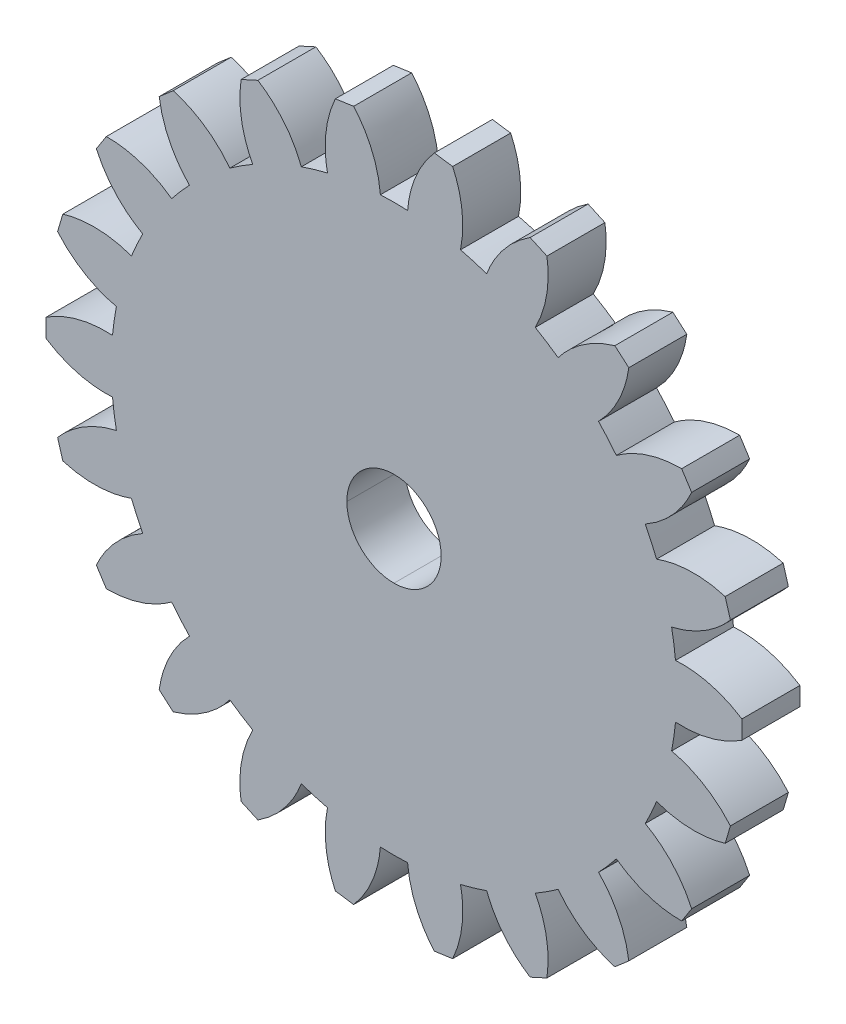
SolidWorks part; units mm, degrees
ref_plane "Alzado" through (0, 0, 0) normal (0, 0, 1) x (1, 0, 0)
ref_plane "Planta" through (0, 0, 0) normal (0, 1, 0) x (1, 0, 0)
ref_plane "Vista lateral" through (0, 0, 0) normal (1, 0, 0) x (0, 0, -1)
sketch "Croquis1" plane through (0, 0, 0) normal (0, 0, 1) x (1, 0, 0)
  spline S120 degree 3 poles (403.5425, -328.4425) (403.5425, -326.6476) (404.9976, -325.1925) (406.7925, -325.1925) knots 0 0 0 0 1 1 1 1
  spline S121 degree 3 poles (406.7925, -325.1925) (408.5874, -325.1925) (410.0425, -326.6476) (410.0425, -328.4425) knots 1 1 1 1 2 2 2 2
  spline S122 degree 3 poles (410.0425, -328.4425) (410.0425, -330.2374) (408.5874, -331.6925) (406.7925, -331.6925) knots 2 2 2 2 3 3 3 3
  spline S123 degree 3 poles (406.7925, -331.6925) (404.9976, -331.6925) (403.5425, -330.2374) (403.5425, -328.4425) knots 3 3 3 3 4 4 4 4
  spline S124 degree 3 poles (396.2468, -350.0015) (396.6282, -350.188) (397.0145, -350.3644) (397.4053, -350.5305) knots 0 0 0 0 1 1 1 1
  spline S125 degree 3 poles (397.4053, -350.5305) (398.7735, -349.6639) (399.8253, -348.3789) (400.4043, -346.8664) knots 0 0 0 0 1 1 1 1
  spline S126 degree 3 poles (400.4043, -346.8664) (400.996, -347.0716) (401.5972, -347.2481) (402.2059, -347.3954) knots 0 0 0 0 1 1 1 1
  spline S127 degree 3 poles (402.2059, -347.3954) (401.8754, -348.9808) (402.0654, -350.6306) (402.7479, -352.0992) knots 0 0 0 0 1 1 1 1
  spline S128 degree 3 poles (402.7479, -352.0992) (403.1664, -352.1708) (403.5868, -352.2312) (404.0085, -352.2805) knots 0 0 0 0 1 1 1 1
  spline S129 degree 3 poles (404.0085, -352.2805) (405.077, -351.0636) (405.7242, -349.5342) (405.8536, -347.9199) knots 0 0 0 0 1 1 1 1
  spline S130 degree 3 poles (405.8536, -347.9199) (406.4792, -347.95) (407.1059, -347.95) (407.7314, -347.9199) knots 0 0 0 0 1 1 1 1
  spline S131 degree 3 poles (407.7314, -347.9199) (407.8608, -349.5342) (408.508, -351.0636) (409.5766, -352.2805) knots 0 0 0 0 1 1 1 1
  spline S132 degree 3 poles (409.5766, -352.2805) (409.9983, -352.2312) (410.4186, -352.1708) (410.8372, -352.0992) knots 0 0 0 0 1 1 1 1
  spline S133 degree 3 poles (410.8372, -352.0992) (411.5196, -350.6306) (411.7097, -348.9808) (411.3791, -347.3954) knots 0 0 0 0 1 1 1 1
  spline S134 degree 3 poles (411.3791, -347.3954) (411.9878, -347.2481) (412.5891, -347.0716) (413.1808, -346.8664) knots 0 0 0 0 1 1 1 1
  spline S135 degree 3 poles (413.1808, -346.8664) (413.7598, -348.3789) (414.8116, -349.6639) (416.1798, -350.5305) knots 0 0 0 0 1 1 1 1
  spline S136 degree 3 poles (416.1798, -350.5305) (416.5705, -350.3644) (416.9568, -350.188) (417.3382, -350.0015) knots 0 0 0 0 1 1 1 1
  spline S137 degree 3 poles (417.3382, -350.0015) (417.5792, -348.4) (417.2968, -346.7636) (416.533, -345.3355) knots 0 0 0 0 1 1 1 1
  spline S138 degree 3 poles (416.533, -345.3355) (417.0755, -345.0227) (417.6027, -344.6839) (418.1126, -344.3203) knots 0 0 0 0 1 1 1 1
  spline S139 degree 3 poles (418.1126, -344.3203) (419.0943, -345.6084) (420.4655, -346.5451) (422.0224, -346.9911) knots 0 0 0 0 1 1 1 1
  spline S140 degree 3 poles (422.0224, -346.9911) (422.3505, -346.7217) (422.6715, -346.4436) (422.9849, -346.1571) knots 0 0 0 0 1 1 1 1
  spline S141 degree 3 poles (422.9849, -346.1571) (422.765, -344.5526) (422.0329, -343.062) (420.8977, -341.907) knots 0 0 0 0 1 1 1 1
  spline S142 degree 3 poles (420.8977, -341.907) (421.3302, -341.454) (421.7405, -340.9804) (422.1274, -340.4879) knots 0 0 0 0 1 1 1 1
  spline S143 degree 3 poles (422.1274, -340.4879) (423.4322, -341.4472) (425.0118, -341.9597) (426.6312, -341.949) knots 0 0 0 0 1 1 1 1
  spline S144 degree 3 poles (426.6312, -341.949) (426.8702, -341.598) (427.0998, -341.2408) (427.3198, -340.8776) knots 0 0 0 0 1 1 1 1
  spline S145 degree 3 poles (427.3198, -340.8776) (426.6567, -339.4001) (425.5344, -338.1761) (424.1198, -337.3877) knots 0 0 0 0 1 1 1 1
  spline S146 degree 3 poles (424.1198, -337.3877) (424.407, -336.8312) (424.6674, -336.2612) (424.8998, -335.6797) knots 0 0 0 0 1 1 1 1
  spline S147 degree 3 poles (424.8998, -335.6797) (426.422, -336.2325) (428.082, -336.2792) (429.6328, -335.8127) knots 0 0 0 0 1 1 1 1
  spline S148 degree 3 poles (429.6328, -335.8127) (429.7633, -335.4086) (429.8829, -335.0011) (429.9916, -334.5907) knots 0 0 0 0 1 1 1 1
  spline S149 degree 3 poles (429.9916, -334.5907) (428.9392, -333.3598) (427.5175, -332.5016) (425.938, -332.1437) knots 0 0 0 0 1 1 1 1
  spline S150 degree 3 poles (425.938, -332.1437) (426.0569, -331.5288) (426.1461, -330.9086) (426.2053, -330.2851) knots 0 0 0 0 1 1 1 1
  spline S151 degree 3 poles (426.2053, -330.2851) (427.8216, -330.3867) (429.4275, -329.9638) (430.7841, -329.0793) knots 0 0 0 0 1 1 1 1
  spline S152 degree 3 poles (430.7841, -329.0793) (430.7953, -328.6548) (430.7953, -328.2302) (430.7841, -327.8057) knots 0 0 0 0 1 1 1 1
  spline S153 degree 3 poles (430.7841, -327.8057) (429.4275, -326.9212) (427.8216, -326.4983) (426.2053, -326.5999) knots 0 0 0 0 1 1 1 1
  spline S154 degree 3 poles (426.2053, -326.5999) (426.1461, -325.9764) (426.0569, -325.3561) (425.938, -324.7413) knots 0 0 0 0 1 1 1 1
  spline S155 degree 3 poles (425.938, -324.7413) (427.5175, -324.3834) (428.9392, -323.5252) (429.9916, -322.2943) knots 0 0 0 0 1 1 1 1
  spline S156 degree 3 poles (429.9916, -322.2943) (429.8829, -321.8839) (429.7633, -321.4764) (429.6328, -321.0723) knots 0 0 0 0 1 1 1 1
  spline S157 degree 3 poles (429.6328, -321.0723) (428.082, -320.6058) (426.422, -320.6525) (424.8998, -321.2053) knots 0 0 0 0 1 1 1 1
  spline S158 degree 3 poles (424.8998, -321.2053) (424.6674, -320.6238) (424.407, -320.0538) (424.1198, -319.4973) knots 0 0 0 0 1 1 1 1
  spline S159 degree 3 poles (424.1198, -319.4973) (425.5344, -318.7089) (426.6567, -317.4849) (427.3198, -316.0074) knots 0 0 0 0 1 1 1 1
  spline S160 degree 3 poles (427.3198, -316.0074) (427.0998, -315.6442) (426.8702, -315.287) (426.6312, -314.936) knots 0 0 0 0 1 1 1 1
  spline S161 degree 3 poles (426.6312, -314.936) (425.0118, -314.9253) (423.4322, -315.4378) (422.1274, -316.3971) knots 0 0 0 0 1 1 1 1
  spline S162 degree 3 poles (422.1274, -316.3971) (421.7405, -315.9046) (421.3302, -315.431) (420.8977, -314.978) knots 0 0 0 0 1 1 1 1
  spline S163 degree 3 poles (420.8977, -314.978) (422.0329, -313.823) (422.765, -312.3324) (422.9849, -310.7279) knots 0 0 0 0 1 1 1 1
  spline S164 degree 3 poles (422.9849, -310.7279) (422.6715, -310.4414) (422.3505, -310.1634) (422.0224, -309.8939) knots 0 0 0 0 1 1 1 1
  spline S165 degree 3 poles (422.0224, -309.8939) (420.4655, -310.3399) (419.0943, -311.2766) (418.1126, -312.5647) knots 0 0 0 0 1 1 1 1
  spline S166 degree 3 poles (418.1126, -312.5647) (417.6027, -312.2011) (417.0755, -311.8623) (416.533, -311.5495) knots 0 0 0 0 1 1 1 1
  spline S167 degree 3 poles (416.533, -311.5495) (417.2968, -310.1215) (417.5792, -308.485) (417.3382, -306.8835) knots 0 0 0 0 1 1 1 1
  spline S168 degree 3 poles (417.3382, -306.8835) (416.9568, -306.697) (416.5705, -306.5206) (416.1798, -306.3545) knots 0 0 0 0 1 1 1 1
  spline S169 degree 3 poles (416.1798, -306.3545) (414.8116, -307.221) (413.7598, -308.5061) (413.1808, -310.0186) knots 0 0 0 0 1 1 1 1
  spline S170 degree 3 poles (413.1808, -310.0186) (412.5891, -309.8134) (411.9878, -309.6369) (411.3791, -309.4896) knots 0 0 0 0 1 1 1 1
  spline S171 degree 3 poles (411.3791, -309.4896) (411.7097, -307.9042) (411.5196, -306.2544) (410.8372, -304.7858) knots 0 0 0 0 1 1 1 1
  spline S172 degree 3 poles (410.8372, -304.7858) (410.4186, -304.7142) (409.9983, -304.6538) (409.5766, -304.6045) knots 0 0 0 0 1 1 1 1
  spline S173 degree 3 poles (409.5766, -304.6045) (408.508, -305.8214) (407.8608, -307.3508) (407.7314, -308.9651) knots 0 0 0 0 1 1 1 1
  spline S174 degree 3 poles (407.7314, -308.9651) (407.1059, -308.935) (406.4792, -308.935) (405.8536, -308.9651) knots 0 0 0 0 1 1 1 1
  spline S175 degree 3 poles (405.8536, -308.9651) (405.7242, -307.3508) (405.077, -305.8214) (404.0085, -304.6045) knots 0 0 0 0 1 1 1 1
  spline S176 degree 3 poles (404.0085, -304.6045) (403.5868, -304.6538) (403.1664, -304.7142) (402.7479, -304.7858) knots 0 0 0 0 1 1 1 1
  spline S177 degree 3 poles (402.7479, -304.7858) (402.0654, -306.2544) (401.8754, -307.9042) (402.2059, -309.4896) knots 0 0 0 0 1 1 1 1
  spline S178 degree 3 poles (402.2059, -309.4896) (401.5972, -309.6369) (400.996, -309.8134) (400.4043, -310.0186) knots 0 0 0 0 1 1 1 1
  spline S179 degree 3 poles (400.4043, -310.0186) (399.8253, -308.5061) (398.7735, -307.221) (397.4053, -306.3545) knots 0 0 0 0 1 1 1 1
  spline S180 degree 3 poles (397.4053, -306.3545) (397.0145, -306.5206) (396.6282, -306.697) (396.2468, -306.8835) knots 0 0 0 0 1 1 1 1
  spline S181 degree 3 poles (396.2468, -306.8835) (396.0058, -308.485) (396.2882, -310.1215) (397.0521, -311.5495) knots 0 0 0 0 1 1 1 1
  spline S182 degree 3 poles (397.0521, -311.5495) (396.5095, -311.8623) (395.9824, -312.2011) (395.4724, -312.5647) knots 0 0 0 0 1 1 1 1
  spline S183 degree 3 poles (395.4724, -312.5647) (394.4908, -311.2766) (393.1195, -310.3399) (391.5626, -309.8939) knots 0 0 0 0 1 1 1 1
  spline S184 degree 3 poles (391.5626, -309.8939) (391.2345, -310.1634) (390.9136, -310.4414) (390.6002, -310.7279) knots 0 0 0 0 1 1 1 1
  spline S185 degree 3 poles (390.6002, -310.7279) (390.8201, -312.3324) (391.5521, -313.823) (392.6873, -314.978) knots 0 0 0 0 1 1 1 1
  spline S186 degree 3 poles (392.6873, -314.978) (392.2549, -315.431) (391.8445, -315.9046) (391.4577, -316.3971) knots 0 0 0 0 1 1 1 1
  spline S187 degree 3 poles (391.4577, -316.3971) (390.1529, -315.4378) (388.5733, -314.9253) (386.9538, -314.936) knots 0 0 0 0 1 1 1 1
  spline S188 degree 3 poles (386.9538, -314.936) (386.7149, -315.287) (386.4853, -315.6442) (386.2653, -316.0074) knots 0 0 0 0 1 1 1 1
  spline S189 degree 3 poles (386.2653, -316.0074) (386.9283, -317.4849) (388.0506, -318.7089) (389.4653, -319.4973) knots 0 0 0 0 1 1 1 1
  spline S190 degree 3 poles (389.4653, -319.4973) (389.178, -320.0538) (388.9177, -320.6238) (388.6852, -321.2053) knots 0 0 0 0 1 1 1 1
  spline S191 degree 3 poles (388.6852, -321.2053) (387.163, -320.6525) (385.503, -320.6058) (383.9522, -321.0723) knots 0 0 0 0 1 1 1 1
  spline S192 degree 3 poles (383.9522, -321.0723) (383.8218, -321.4764) (383.7021, -321.8839) (383.5934, -322.2943) knots 0 0 0 0 1 1 1 1
  spline S193 degree 3 poles (383.5934, -322.2943) (384.6458, -323.5252) (386.0676, -324.3834) (387.647, -324.7413) knots 0 0 0 0 1 1 1 1
  spline S194 degree 3 poles (387.647, -324.7413) (387.5281, -325.3561) (387.4389, -325.9764) (387.3798, -326.5999) knots 0 0 0 0 1 1 1 1
  spline S195 degree 3 poles (387.3798, -326.5999) (385.7635, -326.4983) (384.1576, -326.9212) (382.801, -327.8057) knots 0 0 0 0 1 1 1 1
  spline S196 degree 3 poles (382.801, -327.8057) (382.7897, -328.2302) (382.7897, -328.6548) (382.801, -329.0793) knots 0 0 0 0 1 1 1 1
  spline S197 degree 3 poles (382.801, -329.0793) (384.1576, -329.9638) (385.7635, -330.3867) (387.3798, -330.2851) knots 0 0 0 0 1 1 1 1
  spline S198 degree 3 poles (387.3798, -330.2851) (387.4389, -330.9086) (387.5281, -331.5288) (387.647, -332.1437) knots 0 0 0 0 1 1 1 1
  spline S199 degree 3 poles (387.647, -332.1437) (386.0676, -332.5016) (384.6458, -333.3598) (383.5934, -334.5907) knots 0 0 0 0 1 1 1 1
  spline S200 degree 3 poles (383.5934, -334.5907) (383.7021, -335.0011) (383.8218, -335.4086) (383.9522, -335.8127) knots 0 0 0 0 1 1 1 1
  spline S201 degree 3 poles (383.9522, -335.8127) (385.503, -336.2792) (387.163, -336.2325) (388.6852, -335.6797) knots 0 0 0 0 1 1 1 1
  spline S202 degree 3 poles (388.6852, -335.6797) (388.9177, -336.2612) (389.178, -336.8312) (389.4653, -337.3877) knots 0 0 0 0 1 1 1 1
  spline S203 degree 3 poles (389.4653, -337.3877) (388.0506, -338.1761) (386.9283, -339.4001) (386.2653, -340.8776) knots 0 0 0 0 1 1 1 1
  spline S204 degree 3 poles (386.2653, -340.8776) (386.4853, -341.2408) (386.7149, -341.598) (386.9538, -341.949) knots 0 0 0 0 1 1 1 1
  spline S205 degree 3 poles (386.9538, -341.949) (388.5733, -341.9597) (390.1529, -341.4472) (391.4577, -340.4879) knots 0 0 0 0 1 1 1 1
  spline S206 degree 3 poles (391.4577, -340.4879) (391.8445, -340.9804) (392.2549, -341.454) (392.6873, -341.907) knots 0 0 0 0 1 1 1 1
  spline S207 degree 3 poles (392.6873, -341.907) (391.5521, -343.062) (390.8201, -344.5526) (390.6002, -346.1571) knots 0 0 0 0 1 1 1 1
  spline S208 degree 3 poles (390.6002, -346.1571) (390.9136, -346.4436) (391.2345, -346.7217) (391.5626, -346.9911) knots 0 0 0 0 1 1 1 1
  spline S209 degree 3 poles (391.5626, -346.9911) (393.1195, -346.5451) (394.4908, -345.6084) (395.4724, -344.3203) knots 0 0 0 0 1 1 1 1
  spline S210 degree 3 poles (395.4724, -344.3203) (395.9824, -344.6839) (396.5095, -345.0227) (397.0521, -345.3355) knots 0 0 0 0 1 1 1 1
  spline S211 degree 3 poles (397.0521, -345.3355) (396.2882, -346.7636) (396.0058, -348.4) (396.2468, -350.0015) knots 0 0 0 0 1 1 1 1
extrude "Saliente-Extruir1" add sketch "Croquis1" along normal blind 4
